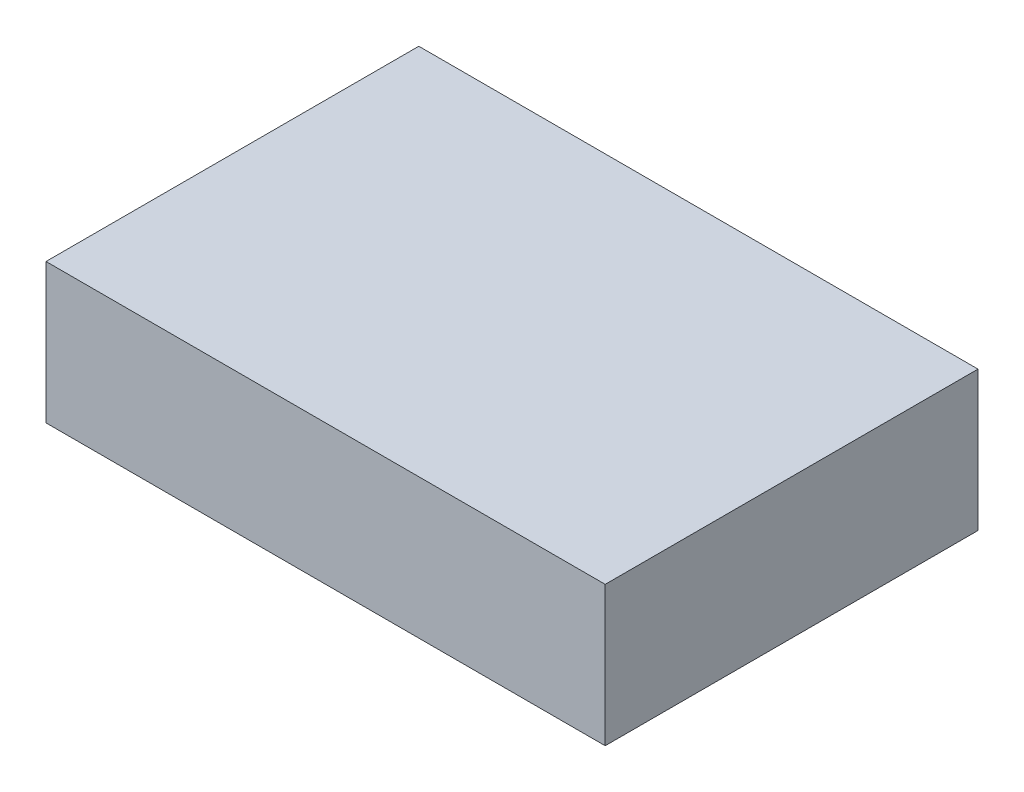
SolidWorks part; units mm, degrees
ref_plane "Front Plane" through (0, 0, 0) normal (0, 0, 1) x (1, 0, 0)
ref_plane "Top Plane" through (0, 0, 0) normal (0, 1, 0) x (1, 0, 0)
ref_plane "Right Plane" through (0, 0, 0) normal (1, 0, 0) x (0, 0, -1)
sketch "Sketch1" plane through (0, 0, 0) normal (0, 1, 0) x (1, 0, 0)
  line L1 (60, -40) -> (-60, -40)
  line L2 (60, -40) -> (60, 40)
  line L3 (60, 40) -> (-60, 40)
  line L4 (-60, -40) -> (-60, 40)
  line L5 (60, -40) -> (-60, 40) construction
  line L6 (60, 40) -> (-60, -40) construction
  point P0 (0, 0)
  dimension "D1" = 80
  dimension "D2" = 120
extrude "Boss-Extrude1" add sketch "Sketch1" along normal blind 30
